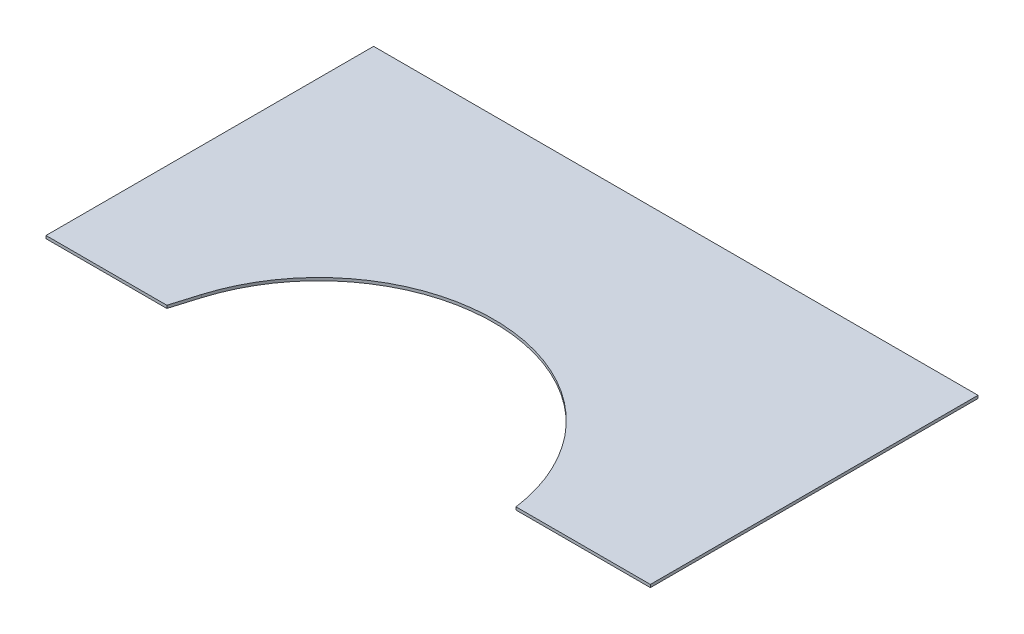
SolidWorks part; units mm, degrees
ref_plane "Front Plane" through (0, 0, 0) normal (0, 0, 1) x (1, 0, 0)
ref_plane "Top Plane" through (0, 0, 0) normal (0, 1, 0) x (1, 0, 0)
ref_plane "Right Plane" through (0, 0, 0) normal (1, 0, 0) x (0, 0, -1)
sketch "Sketch1" plane through (0, 0, 0) normal (0, 1, 0) x (1, 0, 0)
  line L0 (0, 368.3) -> (679.45, 368.3)
  line L1 (0, 0) -> (679.45, 0)
  line L2 (0, 0) -> (0, 368.3)
  line L4 (679.45, 0) -> (679.45, 368.3)
  dimension "D1" = 368.3
  dimension "D2" = 679.45
extrude "Boss-Extrude1" add sketch "Sketch1" along normal blind 3.175
sketch "Sketch2" plane through (0, 3.175, 0) normal (0, 1, 0) x (1, 0, 0)
  line L12 (135.833, 0) -> (144.9434, 30.1431)
  line L13 (0, 0) -> (679.45, 0) construction
  line L14 (135.833, 0) -> (488.6676, 0)
  arc A8 (494.6251, -139.7168) -> (530.1226, -33.1583) centre (333.375, -26.8083) ccw construction
  arc A10 (327.025, 169.9393) -> (144.9434, 30.1431) centre (333.375, -26.8083) ccw construction
  arc A11 (530.1226, -33.1583) -> (327.025, 169.9393) centre (333.375, -26.8083) ccw construction
  arc A12 (494.6251, -139.7168) -> (530.1226, -33.1583) centre (333.375, -26.8083) ccw
  arc A14 (327.025, 169.9393) -> (144.9434, 30.1431) centre (333.375, -26.8083) ccw
  arc A15 (530.1226, -33.1583) -> (327.025, 169.9393) centre (333.375, -26.8083) ccw
  spline S0 degree 3 poles (579.0964, 856.7076) (461.012, 14.849) (536.0415, -102.4122) (484.7792, -150.2338) (475.3357, -156.2316) (461.5217, -161.4443) (336.0356, -185.9928) (128.9981, -11.9673) (1337.1517, 258.4834) knots -0.818542 -0.818542 -0.818542 -0.818542 0.027722 0.055445 0.110889 0.166334 0.221779 1.450191 1.450191 1.450191 1.450191 only from (494.6251, -139.7168) to (431.2444, -164.9838) construction
  spline S1 degree 3 poles (494.6251, -139.7168) (493.4573, -141.3846) (490.8952, -144.5283) (484.7792, -150.2338) (475.3357, -156.2316) (461.5217, -161.4443) (379.6484, -177.461) (267.7224, -112.1878) (488.6676, 0) knots 0 0 0 0 0.027722 0.055445 0.110889 0.166334 0.221779 0.984715 0.984715 0.984715 0.984715
  dimension "D1" = 196.85
extrude "Cut-Extrude1" cut sketch "Sketch2" against normal through all
